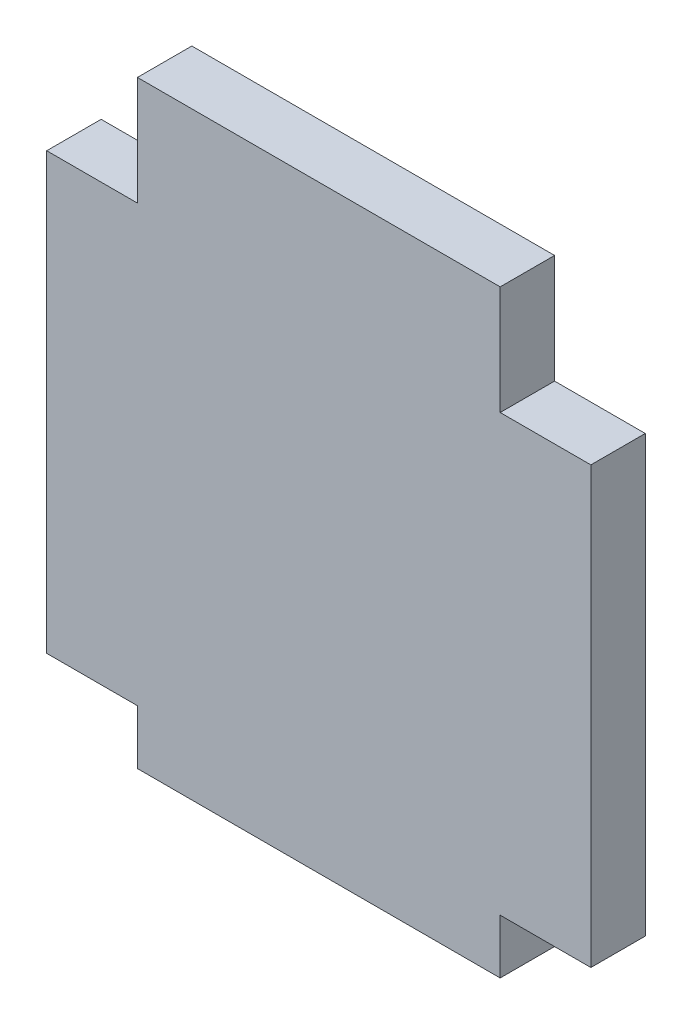
SolidWorks part; units mm, degrees
material "MDF"
ref_plane "Plano frontal" through (0, 0, 0) normal (0, 0, 1) x (1, 0, 0)
ref_plane "Plano superior" through (0, 0, 0) normal (0, 1, 0) x (1, 0, 0)
ref_plane "Plano direito" through (0, 0, 0) normal (1, 0, 0) x (0, 0, -1)
sketch "Esboço1" plane through (0, 0, 0) normal (0, 0, 1) x (1, 0, 0)
  line L0 (0, 0) -> (15, 0) construction
  line L1 (-15, -12) -> (15, -12)
  line L2 (-15, -12) -> (-15, 12)
  line L3 (-15, 12) -> (15, 12)
  line L4 (15, -12) -> (15, 12)
  line L5 (-15, -12) -> (15, 12) construction
  line L6 (-15, 12) -> (15, -12) construction
  line L7 (10, 18) -> (-10, 18)
  line L8 (10, 18) -> (10, 12)
  line L9 (10, 12) -> (-10, 12)
  line L10 (-10, 18) -> (-10, 12)
  line L11 (10, 18) -> (-10, 12) construction
  line L12 (10, 12) -> (-10, 18) construction
  line L13 (10, -12) -> (-10, -12)
  line L14 (-10, -15) -> (-10, -12)
  line L15 (10, -15) -> (-10, -15)
  line L16 (10, -15) -> (10, -12)
  point P0 (0, 0)
  point P6 (0, 15)
  dimension "D1" = 3
  dimension "D2" = 20
  dimension "D3" = 30
  dimension "D4" = 24
  dimension "D5" = 6
extrude "Ressalto-extrusão1" add sketch "Esboço1" along normal blind 3 contours L1 L4 L3 L2 | L7 L10 L3 L8 | L15 L16 L1 L14
